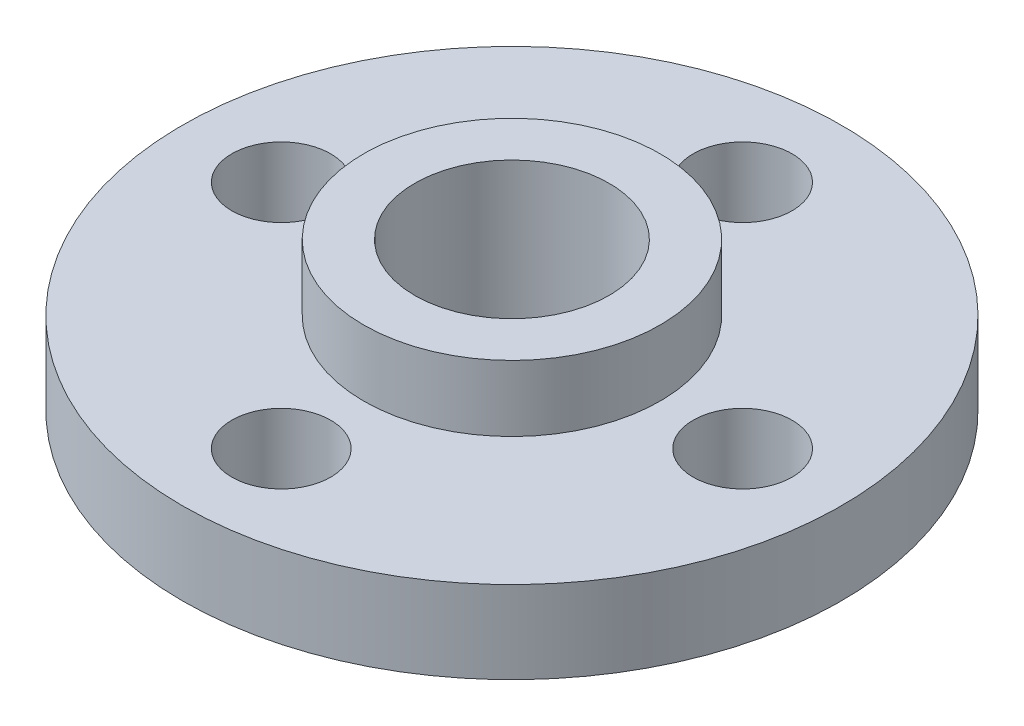
SolidWorks part; units mm, degrees
material "1060 Сплав"
ref_plane "Спереди" through (0, 0, 0) normal (0, 0, 1) x (1, 0, 0)
ref_plane "Сверху" through (0, 0, 0) normal (0, 1, 0) x (1, 0, 0)
ref_plane "Справа" through (0, 0, 0) normal (1, 0, 0) x (0, 0, -1)
sketch "Эскиз1" plane through (0, 0, 0) normal (0, 1, 0) x (1, 0, 0)
  circle A0 centre (0, 0) radius 10
  circle A1 centre (-7, 0) radius 1.5
  circle A2 centre (0, 7) radius 1.5
  circle A3 centre (0, -7) radius 1.5
  circle A4 centre (7, 0) radius 1.5
  circle A5 centre (0, 0) radius 2.95
  dimension "D1" = 20
  dimension "D2" = 3
  dimension "D3" = 3
  dimension "D4" = 3
  dimension "D5" = 3
  dimension "D10" = 5.9
  dimension "D6" = 7
  dimension "D7" = 14
  dimension "D8" = 7
  dimension "D9" = 14
extrude "Бобышка-Вытянуть1" add sketch "Эскиз1" along normal blind 2.5
sketch "Эскиз2" plane through (0, 2.5, 0) normal (0, 1, 0) x (1, 0, 0)
  circle A0 centre (0, 0) radius 2.95
  circle A1 centre (0, 0) radius 4.5
  dimension "D1" = 9
extrude "Бобышка-Вытянуть2" add sketch "Эскиз2" along normal blind 2
